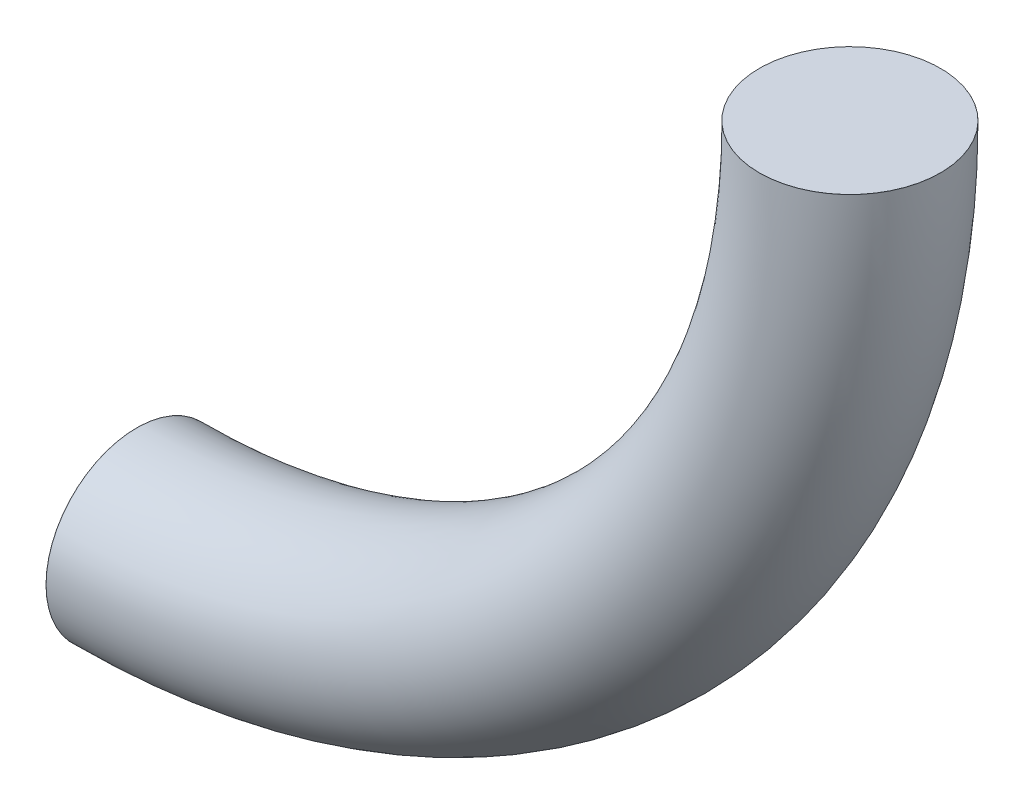
SolidWorks part; units mm, degrees
ref_plane "Alzado" through (0, 0, 0) normal (0, 0, 1) x (1, 0, 0)
ref_plane "Planta" through (0, 0, 0) normal (0, 1, 0) x (1, 0, 0)
ref_plane "Vista lateral" through (0, 0, 0) normal (1, 0, 0) x (0, 0, -1)
sketch "Croquis3" plane through (0, 0, 0) normal (0, 1, 0) x (1, 0, 0)
  circle A0 centre (0, 0) radius 6.35
  dimension "D1" = 12.7
sketch "Croquis4" plane through (0, 0, 0) normal (0, 0, 1) x (1, 0, 0)
  line L0 (0, 0) -> (0, -0.01)
  line L1 (-50, -50.01) -> (-50.01, -50.01)
  arc A0 (0, -0.01) -> (-50, -50.01) centre (-50, -0.01) cw
  point P6 (0, -50.01)
  dimension "D3" = 50
  dimension "D1" = 50.01
  dimension "D2" = 50.01
sweep "Barrer1" add profiles "Croquis3" path "Croquis4"
